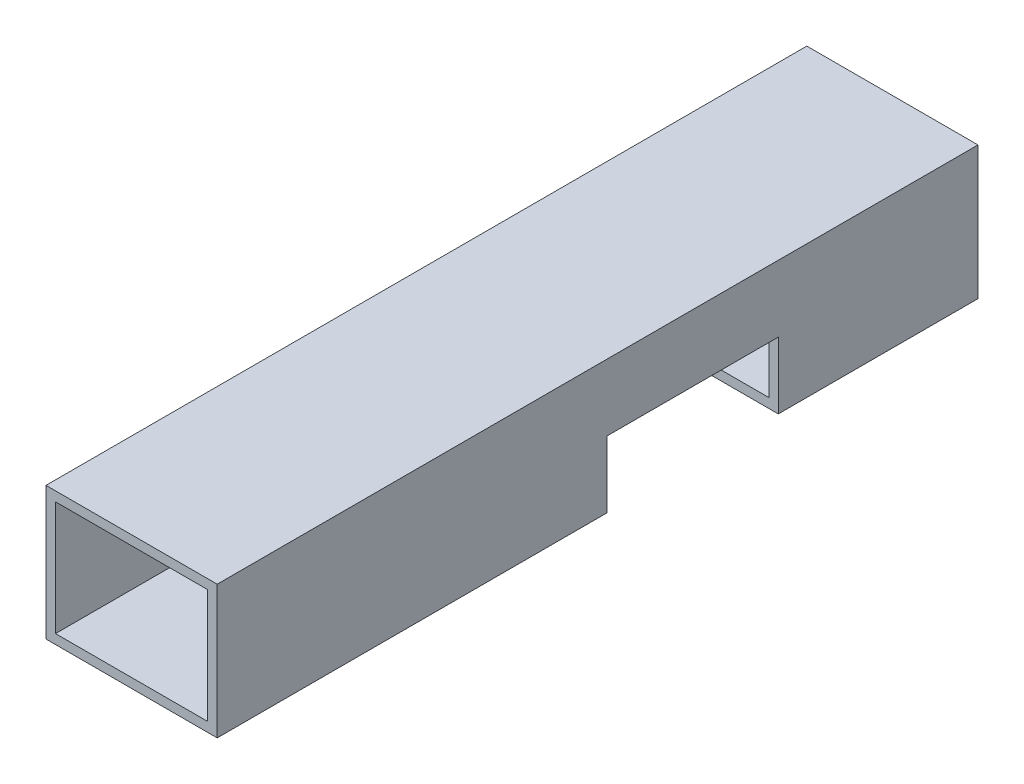
SolidWorks part; units mm, degrees
ref_plane "Plan de face" through (0, 0, 0) normal (0, 0, 1) x (1, 0, 0)
ref_plane "Plan de dessus" through (0, 0, 0) normal (0, 1, 0) x (1, 0, 0)
ref_plane "Plan de droite" through (0, 0, 0) normal (1, 0, 0) x (0, 0, -1)
sketch "Esquisse1" plane through (0, 0, 0) normal (0, 0, 1) x (1, 0, 0)
  line L0 (0, 7) -> (9, 0) construction
  line L1 (0, 0) -> (9, 0)
  line L2 (0, 0) -> (0, 7)
  line L3 (0, 7) -> (9, 7)
  line L4 (9, 0) -> (9, 7)
  line L6 (0.5, 0.5) -> (8.5, 0.5)
  line L7 (0.5, 0.5) -> (0.5, 6.5)
  line L8 (0.5, 6.5) -> (8.5, 6.5)
  line L9 (8.5, 0.5) -> (8.5, 6.5)
  line L10 (0.5, 0.5) -> (8.5, 6.5) construction
  line L11 (9, 7) -> (0, 0) construction
  line L12 (0.5, 6.5) -> (8.5, 0.5) construction
  point P4 (4.5, 3.5)
  dimension "D1" = 7
  dimension "D2" = 9
  dimension "D3" = 8
  dimension "D4" = 6
extrude "Boss.-Extru.1" add sketch "Esquisse1" along normal blind 40
ref_plane "Plan1" through (9, 0, 40) normal (0, 0, -1) x (-1, 0, 0)
sketch "Esquisse4" plane through (9, 0, 0) normal (1, 0, 0) x (0, 0, -1)
  line L0 (-40, -5.6375) -> (-40, 5.6375) construction
  line L1 (-40, 0) -> (0, 0) construction
  line L8 (-19.5, 0) -> (-10.5, 0)
  line L9 (-19.5, 0) -> (-19.5, 3.5)
  line L10 (-19.5, 3.5) -> (-10.5, 3.5)
  line L11 (-10.5, 0) -> (-10.5, 3.5)
  dimension "D1" = 20.5
  dimension "D2" = 9
  dimension "D3" = 3.5
extrude "Enlèv. mat.-Extru.1" cut sketch "Esquisse4" against normal blind 50
